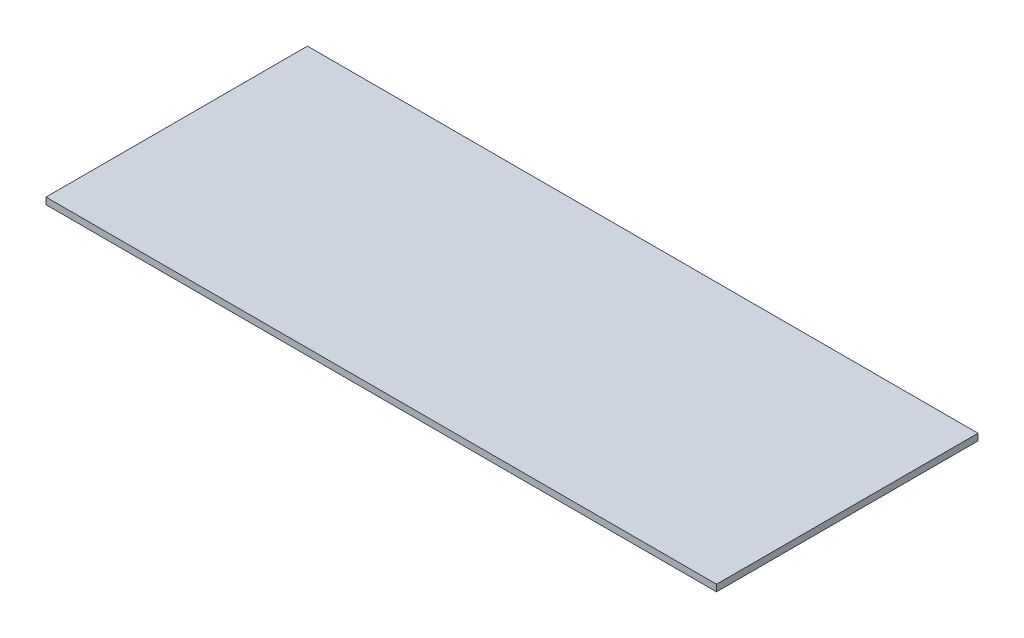
SolidWorks part; units mm, degrees
material "Hexcel AS4C (3000 Filaments)"
ref_plane "Front Plane" through (0, 0, 0) normal (0, 0, 1) x (1, 0, 0)
ref_plane "Top Plane" through (0, 0, 0) normal (0, 1, 0) x (1, 0, 0)
ref_plane "Right Plane" through (0, 0, 0) normal (1, 0, 0) x (0, 0, -1)
sketch "Sketch1" plane through (0, 0, 0) normal (0, 1, 0) x (1, 0, 0)
  line L1 (-276.9436, 133.3716) -> (128.3936, 133.3716)
  line L2 (-276.9436, 133.3716) -> (-276.9436, -26.6284)
  line L3 (-276.9436, -26.6284) -> (128.3936, -26.6284)
  line L4 (128.3936, 133.3716) -> (128.3936, -26.6284)
  line L5 (-276.9436, 133.3716) -> (128.3936, -26.6284) construction
  line L6 (-276.9436, -26.6284) -> (128.3936, 133.3716) construction
  point P0 (-74.275, 53.3716)
  dimension "D1" = 405.3372
  dimension "D2" = 160
extrude "Boss-Extrude1" add sketch "Sketch1" along normal blind 4
sketch "Sketch2" plane through (0, 0, 26.6284) normal (0, 0, 1) x (1, 0, 0)
  line L0 (-276.9436, 4) -> (128.3936, 4) construction
  line L1 (128.3936, 0) -> (124.8936, 0)
  line L2 (128.3936, 0) -> (128.3936, 4)
  line L3 (128.3936, 4) -> (124.8936, 4)
  line L4 (124.8936, 0) -> (124.8936, 4)
  dimension "D1" = 3.5
extrude "Cut-Extrude2" cut sketch "Sketch2" against normal blind 184
sketch "Sketch3" plane through (0, 0, 26.6284) normal (0, 0, 1) x (1, 0, 0)
  line L1 (124.8936, 0) -> (122.8936, 0)
  line L2 (124.8936, 0) -> (124.8936, 4)
  line L3 (124.8936, 4) -> (122.8936, 4)
  line L4 (122.8936, 0) -> (122.8936, 4)
  dimension "D1" = 4
  dimension "D2" = 2
extrude "Cut-Extrude3" cut sketch "Sketch3" against normal blind 184
scale "Scale1" scale about centroid uniform scaling yes scale factor 1.01875
sketch "Sketch4" plane through (0, 0, 28.1284) normal (0, 0, 1) x (1, 0, 0)
  line L0 (-280.6921, 4.0375) -> (126.6421, 4.0375) construction
  line L1 (126.6421, -0.0375) -> (121.6421, -0.0375)
  line L2 (126.6421, -0.0375) -> (126.6421, 4.0375)
  line L3 (126.6421, 4.0375) -> (121.6421, 4.0375)
  line L4 (121.6421, -0.0375) -> (121.6421, 4.0375)
  dimension "D1" = 5
extrude "Cut-Extrude4" cut sketch "Sketch4" against normal blind 220 contours L2 L1 L4 L3
sketch "Sketch5" plane through (-280.6921, 0, 0) normal (-1, 0, 0) x (0, 0, 1)
  line L0 (-134.8716, 4.0375) -> (28.1284, 4.0375) construction
  line L1 (-134.8716, -0.0375) -> (-134.3716, -0.0375)
  line L2 (-134.8716, -0.0375) -> (-134.8716, 4.0375)
  line L3 (-134.8716, 4.0375) -> (-134.3716, 4.0375)
  line L4 (-134.3716, -0.0375) -> (-134.3716, 4.0375)
  dimension "D1" = 0.5
extrude "Cut-Extrude5" cut sketch "Sketch5" against normal blind 430 contours L2 L1 L4 L3
sketch "Sketch6" plane through (-280.6921, 0, 0) normal (-1, 0, 0) x (0, 0, 1)
  line L0 (-134.3716, 4.0375) -> (28.1284, 4.0375) construction
  line L1 (28.1284, -0.0375) -> (27.1284, -0.0375)
  line L2 (28.1284, -0.0375) -> (28.1284, 4.0375)
  line L3 (28.1284, 4.0375) -> (27.1284, 4.0375)
  line L4 (27.1284, -0.0375) -> (27.1284, 4.0375)
  dimension "D1" = 1
extrude "Cut-Extrude6" cut sketch "Sketch6" against normal blind 430
sketch "Sketch7" plane through (-280.6921, 0, 0) normal (-1, 0, 0) x (0, 0, 1)
  line L0 (-134.3716, 4.0375) -> (27.1284, 4.0375) construction
  line L1 (27.1284, -0.0375) -> (26.6284, -0.0375)
  line L2 (27.1284, -0.0375) -> (27.1284, 4.0375)
  line L3 (27.1284, 4.0375) -> (26.6284, 4.0375)
  line L4 (26.6284, -0.0375) -> (26.6284, 4.0375)
  dimension "D1" = 0.5
extrude "Cut-Extrude7" cut sketch "Sketch7" against normal blind 430
sketch "Sketch8" plane through (-280.6921, 0, 0) normal (-1, 0, 0) x (0, 0, 1)
  line L0 (-134.3716, -0.0375) -> (26.6284, -0.0375) construction
  line L1 (-134.3716, 4.0375) -> (-133.3716, 4.0375)
  line L2 (-134.3716, 4.0375) -> (-134.3716, -0.0375)
  line L3 (-134.3716, -0.0375) -> (-133.3716, -0.0375)
  line L4 (-133.3716, 4.0375) -> (-133.3716, -0.0375)
  dimension "D1" = 1
extrude "Cut-Extrude8" cut sketch "Sketch8" against normal blind 430
sketch "Sketch9" plane through (-280.6921, 0, 0) normal (-1, 0, 0) x (0, 0, 1)
  line L1 (-133.3716, -0.0375) -> (26.6284, -0.0375)
  line L2 (-133.3716, -0.0375) -> (-133.3716, 4.0375)
  line L3 (-133.3716, 4.0375) -> (26.6284, 4.0375)
  line L4 (26.6284, -0.0375) -> (26.6284, 4.0375)
extrude "Boss-Extrude2" add sketch "Sketch9" along normal blind 6
sketch "Sketch11" plane through (0, 0, -133.3716) normal (0, 0, -1) x (-1, 0, 0)
  line L1 (286.6921, -0.0375) -> (-121.6421, -0.0375)
  line L2 (286.6921, -0.0375) -> (286.6921, 4.0375)
  line L3 (286.6921, 4.0375) -> (-121.6421, 4.0375)
  line L4 (-121.6421, -0.0375) -> (-121.6421, 4.0375)
extrude "Boss-Extrude4" add sketch "Sketch11" along normal blind 3
sketch "Sketch12" plane through (121.6421, 0, 0) normal (1, 0, 0) x (0, 0, -1)
  line L1 (-26.6284, -0.0375) -> (136.3716, -0.0375)
  line L2 (-26.6284, -0.0375) -> (-26.6284, 4.0375)
  line L3 (-26.6284, 4.0375) -> (136.3716, 4.0375)
  line L4 (136.3716, -0.0375) -> (136.3716, 4.0375)
extrude "Boss-Extrude5" add sketch "Sketch12" along normal blind 2
sketch "Sketch13" plane through (0, 0, -136.3716) normal (0, 0, -1) x (-1, 0, 0)
  line L1 (-123.6421, -0.0375) -> (286.6921, -0.0375)
  line L2 (-123.6421, -0.0375) -> (-123.6421, 4.0375)
  line L3 (-123.6421, 4.0375) -> (286.6921, 4.0375)
  line L4 (286.6921, -0.0375) -> (286.6921, 4.0375)
extrude "Cut-Extrude9" cut sketch "Sketch13" against normal blind 3
